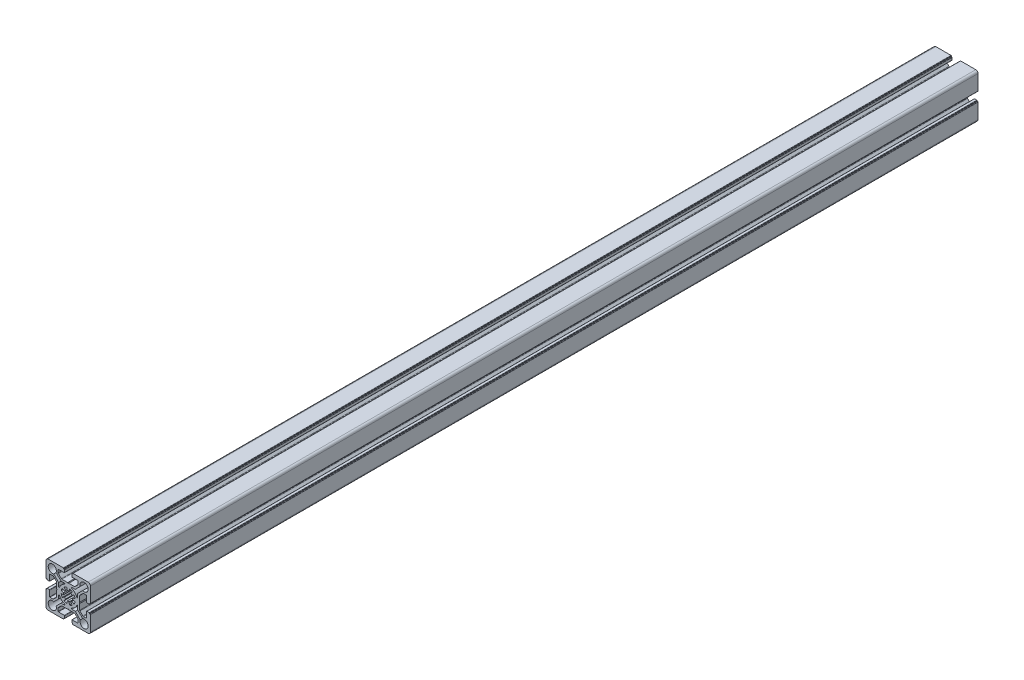
SolidWorks part; units mm, degrees
material "6063 T5"
ref_plane "Спереди" through (0, 0, 0) normal (0, 0, 1) x (1, 0, 0)
ref_plane "Сверху" through (0, 0, 0) normal (0, 1, 0) x (1, 0, 0)
ref_plane "Справа" through (0, 0, 0) normal (1, 0, 0) x (0, 0, -1)
sketch "Эскиз2" plane through (0, 0, 0) normal (0, 0, 1) x (1, 0, 0)
  line L0 (0, 0) -> (-21.2527, 21.2527) construction
  line L1 (-10.7, 8.013) -> (-10.7, 4.1183)
  line L2 (-10.7, 8.013) -> (-16.2812, 13.5942)
  line L3 (-8.013, 10.7) -> (-13.5942, 16.2812)
  line L4 (-8.013, 10.7) -> (-4.1183, 10.7)
  line L5 (10.7, 8.013) -> (16.2812, 13.5942)
  line L6 (10.7, 8.013) -> (10.7, 4.1183)
  line L7 (8.013, 10.7) -> (4.1183, 10.7)
  line L8 (8.013, 10.7) -> (13.5942, 16.2812)
  line L9 (8.013, -10.7) -> (13.5942, -16.2812)
  line L10 (8.013, -10.7) -> (4.1183, -10.7)
  line L11 (10.7, -8.013) -> (10.7, -4.1183)
  line L12 (10.7, -8.013) -> (16.2812, -13.5942)
  line L13 (-10.7, -8.013) -> (-16.2812, -13.5942)
  line L14 (-10.7, -8.013) -> (-10.7, -4.1183)
  line L15 (-8.013, -10.7) -> (-4.1183, -10.7)
  line L16 (-8.013, -10.7) -> (-13.5942, -16.2812)
  line L17 (-25, 11.3) -> (-25, 22.5)
  line L18 (-22.5, 25) -> (-11.3, 25)
  line L19 (11.3, 25) -> (22.5, 25)
  line L20 (25, 22.5) -> (25, 11.3)
  line L21 (25, -11.3) -> (25, -22.5)
  line L22 (22.5, -25) -> (11.3, -25)
  line L23 (-11.3, -25) -> (-22.5, -25)
  line L24 (-25, -22.5) -> (-25, -11.3)
  arc A2 (-3.9311, 9.7364) -> (-9.7364, 3.9311) centre (0, 0) ccw
  arc A3 (-9.7364, 3.9311) -> (-10.7, 4.1183) centre (-10.2, 4.1183) cw
  arc A4 (-16.2812, 13.5942) -> (-13.5942, 16.2812) centre (-17.9, 17.9) cw
  arc A5 (-3.9311, 9.7364) -> (-4.1183, 10.7) centre (-4.1183, 10.2) ccw
  arc A6 (13.5942, 16.2812) -> (16.2812, 13.5942) centre (17.9, 17.9) cw
  arc A7 (9.7364, 3.9311) -> (10.7, 4.1183) centre (10.2, 4.1183) ccw
  arc A8 (9.7364, 3.9311) -> (3.9311, 9.7364) centre (0, 0) ccw
  arc A9 (3.9311, 9.7364) -> (4.1183, 10.7) centre (4.1183, 10.2) cw
  arc A10 (16.2812, -13.5942) -> (13.5942, -16.2812) centre (17.9, -17.9) cw
  arc A11 (3.9311, -9.7364) -> (4.1183, -10.7) centre (4.1183, -10.2) ccw
  arc A12 (3.9311, -9.7364) -> (9.7364, -3.9311) centre (0, 0) ccw
  arc A13 (9.7364, -3.9311) -> (10.7, -4.1183) centre (10.2, -4.1183) cw
  arc A14 (-13.5942, -16.2812) -> (-16.2812, -13.5942) centre (-17.9, -17.9) cw
  arc A15 (-9.7364, -3.9311) -> (-10.7, -4.1183) centre (-10.2, -4.1183) ccw
  arc A16 (-9.7364, -3.9311) -> (-3.9311, -9.7364) centre (0, 0) ccw
  arc A17 (-3.9311, -9.7364) -> (-4.1183, -10.7) centre (-4.1183, -10.2) cw
  arc A18 (-25, 22.5) -> (-22.5, 25) centre (-22.5, 22.5) cw
  arc A19 (22.5, 25) -> (25, 22.5) centre (22.5, 22.5) cw
  arc A20 (25, -22.5) -> (22.5, -25) centre (22.5, -22.5) cw
  arc A21 (-22.5, -25) -> (-25, -22.5) centre (-22.5, -22.5) cw
  point P50 (0, 0)
  point P71 (0, 0)
  line B0 (-25, 11.3) -> (-25, 5.4)
  line B1 (-24.7, 5.1) -> (-24, 5.1)
  line B2 (-24, 5.1) -> (-24, 4.4)
  line B3 (-23.7, 4.1) -> (-21.1, 4.1)
  line B4 (-20.8, 4.4) -> (-20.8, 11)
  line B5 (-20.5, 11.3) -> (-17.2142, 11.3)
  line B6 (-16.5071, 11.0071) -> (-13.2929, 7.7929)
  line B7 (-13, 7.0858) -> (-13, 0.6)
  line B8 (-13, 0) -> (-25, 0) construction
  line B9 (-16.5071, -11.0071) -> (-13.2929, -7.7929)
  line B10 (-20.5, -11.3) -> (-17.2142, -11.3)
  line B11 (-20.8, -4.4) -> (-20.8, -11)
  line B12 (-23.7, -4.1) -> (-21.1, -4.1)
  line B13 (-24, -5.1) -> (-24, -4.4)
  line B14 (-24.7, -5.1) -> (-24, -5.1)
  line B15 (-25, -11.3) -> (-25, -5.4)
  line B16 (-13, 0.6) -> (-12.4, 0)
  line B17 (-12.4, 0) -> (-13, -0.6)
  line B18 (-13, -0.6) -> (-13, -7.0858)
  arc B19 (-21.1, 4.1) -> (-20.8, 4.4) centre (-21.1, 4.4) ccw
  arc B20 (-24, 4.4) -> (-23.7, 4.1) centre (-23.7, 4.4) ccw
  arc B21 (-25, 5.4) -> (-24.7, 5.1) centre (-24.7, 5.4) ccw
  arc B22 (-13.2929, 7.7929) -> (-13, 7.0858) centre (-14, 7.0858) cw
  arc B23 (-17.2142, 11.3) -> (-16.5071, 11.0071) centre (-17.2142, 10.3) cw
  arc B24 (-17.2142, -11.3) -> (-16.5071, -11.0071) centre (-17.2142, -10.3) ccw
  arc B25 (-13.2929, -7.7929) -> (-13, -7.0858) centre (-14, -7.0858) ccw
  arc B26 (-25, -5.4) -> (-24.7, -5.1) centre (-24.7, -5.4) cw
  arc B27 (-24, -4.4) -> (-23.7, -4.1) centre (-23.7, -4.4) cw
  arc B28 (-21.1, -4.1) -> (-20.8, -4.4) centre (-21.1, -4.4) cw
  arc B29 (-20.5, -11.3) -> (-20.8, -11) centre (-20.5, -11) cw
  arc B30 (-20.8, 11) -> (-20.5, 11.3) centre (-20.5, 11) cw
  line B31 (0, 0) -> (3.6062, 3.6062) construction
  line B32 (1.4579, 7.866) -> (0.9294, 5.0146)
  line B33 (2.8887, 4.203) -> (4.5312, 6.593)
  line B34 (0, 0) -> (0, 5.1) construction
  arc B35 (0.9294, -5.0146) -> (-0.9294, -5.0146) centre (0, 0) cw
  arc B36 (-6.593, -4.5312) -> (-7.866, -1.4579) centre (0, 0) cw
  arc B37 (4.203, 2.8887) -> (2.8887, 4.203) centre (0, 0) ccw
  arc B38 (4.5312, 6.593) -> (1.4579, 7.866) centre (0, 0) ccw
  arc B39 (0.9294, 5.0146) -> (-0.9294, 5.0146) centre (0, 0) ccw
  line B40 (-1.4579, 7.866) -> (-0.9294, 5.0146)
  arc B41 (4.5312, -6.593) -> (1.4579, -7.866) centre (0, 0) cw
  arc B42 (-4.203, -2.8887) -> (-2.8887, -4.203) centre (0, 0) ccw
  line B43 (-2.8887, -4.203) -> (-4.5312, -6.593)
  line B44 (0, 0) -> (6.3318, 0) construction
  line B45 (4.203, 2.8887) -> (6.593, 4.5312)
  line B46 (7.866, 1.4579) -> (5.0146, 0.9294)
  line B47 (-7.866, 1.4579) -> (-5.0146, 0.9294)
  line B48 (-4.203, 2.8887) -> (-6.593, 4.5312)
  line B49 (-2.8887, 4.203) -> (-4.5312, 6.593)
  line B50 (7.866, -1.4579) -> (5.0146, -0.9294)
  line B51 (4.203, -2.8887) -> (6.593, -4.5312)
  line B52 (2.8887, -4.203) -> (4.5312, -6.593)
  line B53 (1.4579, -7.866) -> (0.9294, -5.0146)
  line B54 (-1.4579, -7.866) -> (-0.9294, -5.0146)
  line B55 (-4.203, -2.8887) -> (-6.593, -4.5312)
  line B56 (-7.866, -1.4579) -> (-5.0146, -0.9294)
  arc B57 (5.0146, 0.9294) -> (5.0146, -0.9294) centre (0, 0) cw
  arc B58 (6.593, 4.5312) -> (7.866, 1.4579) centre (0, 0) cw
  arc B59 (-5.0146, 0.9294) -> (-5.0146, -0.9294) centre (0, 0) ccw
  arc B60 (-6.593, 4.5312) -> (-7.866, 1.4579) centre (0, 0) ccw
  arc B61 (-4.203, 2.8887) -> (-2.8887, 4.203) centre (0, 0) cw
  arc B62 (-4.5312, 6.593) -> (-1.4579, 7.866) centre (0, 0) cw
  arc B63 (6.593, -4.5312) -> (7.866, -1.4579) centre (0, 0) ccw
  arc B64 (4.203, -2.8887) -> (2.8887, -4.203) centre (0, 0) cw
  arc B65 (-4.5312, -6.593) -> (-1.4579, -7.866) centre (0, 0) ccw
  line B66 (11.3, 25) -> (5.4, 25)
  line B67 (5.1, 24.7) -> (5.1, 24)
  line B68 (5.1, 24) -> (4.4, 24)
  line B69 (4.1, 23.7) -> (4.1, 21.1)
  line B70 (4.4, 20.8) -> (11, 20.8)
  line B71 (11.3, 20.5) -> (11.3, 17.2142)
  line B72 (11.0071, 16.5071) -> (7.7929, 13.2929)
  line B73 (7.0858, 13) -> (0.6, 13)
  line B74 (0, 13) -> (0, 25) construction
  line B75 (-11.0071, 16.5071) -> (-7.7929, 13.2929)
  line B76 (-11.3, 20.5) -> (-11.3, 17.2142)
  line B77 (-4.4, 20.8) -> (-11, 20.8)
  line B78 (-4.1, 23.7) -> (-4.1, 21.1)
  line B79 (-5.1, 24) -> (-4.4, 24)
  line B80 (-5.1, 24.7) -> (-5.1, 24)
  line B81 (-11.3, 25) -> (-5.4, 25)
  line B82 (0.6, 13) -> (0, 12.4)
  line B83 (0, 12.4) -> (-0.6, 13)
  line B84 (-0.6, 13) -> (-7.0858, 13)
  arc B85 (4.1, 21.1) -> (4.4, 20.8) centre (4.4, 21.1) ccw
  arc B86 (4.4, 24) -> (4.1, 23.7) centre (4.4, 23.7) ccw
  arc B87 (5.4, 25) -> (5.1, 24.7) centre (5.4, 24.7) ccw
  arc B88 (7.7929, 13.2929) -> (7.0858, 13) centre (7.0858, 14) cw
  arc B89 (11.3, 17.2142) -> (11.0071, 16.5071) centre (10.3, 17.2142) cw
  arc B90 (-11.3, 17.2142) -> (-11.0071, 16.5071) centre (-10.3, 17.2142) ccw
  arc B91 (-7.7929, 13.2929) -> (-7.0858, 13) centre (-7.0858, 14) ccw
  arc B92 (-5.4, 25) -> (-5.1, 24.7) centre (-5.4, 24.7) cw
  arc B93 (-4.4, 24) -> (-4.1, 23.7) centre (-4.4, 23.7) cw
  arc B94 (-4.1, 21.1) -> (-4.4, 20.8) centre (-4.4, 21.1) cw
  arc B95 (-11.3, 20.5) -> (-11, 20.8) centre (-11, 20.5) cw
  arc B96 (11, 20.8) -> (11.3, 20.5) centre (11, 20.5) cw
  line B97 (25, -11.3) -> (25, -5.4)
  line B98 (24.7, -5.1) -> (24, -5.1)
  line B99 (24, -5.1) -> (24, -4.4)
  line B100 (23.7, -4.1) -> (21.1, -4.1)
  line B101 (20.8, -4.4) -> (20.8, -11)
  line B102 (20.5, -11.3) -> (17.2142, -11.3)
  line B103 (16.5071, -11.0071) -> (13.2929, -7.7929)
  line B104 (13, -7.0858) -> (13, -0.6)
  line B105 (13, 0) -> (25, 0) construction
  line B106 (16.5071, 11.0071) -> (13.2929, 7.7929)
  line B107 (20.5, 11.3) -> (17.2142, 11.3)
  line B108 (20.8, 4.4) -> (20.8, 11)
  line B109 (23.7, 4.1) -> (21.1, 4.1)
  line B110 (24, 5.1) -> (24, 4.4)
  line B111 (24.7, 5.1) -> (24, 5.1)
  line B112 (25, 11.3) -> (25, 5.4)
  line B113 (13, -0.6) -> (12.4, 0)
  line B114 (12.4, 0) -> (13, 0.6)
  line B115 (13, 0.6) -> (13, 7.0858)
  arc B116 (21.1, -4.1) -> (20.8, -4.4) centre (21.1, -4.4) ccw
  arc B117 (24, -4.4) -> (23.7, -4.1) centre (23.7, -4.4) ccw
  arc B118 (25, -5.4) -> (24.7, -5.1) centre (24.7, -5.4) ccw
  arc B119 (13.2929, -7.7929) -> (13, -7.0858) centre (14, -7.0858) cw
  arc B120 (17.2142, -11.3) -> (16.5071, -11.0071) centre (17.2142, -10.3) cw
  arc B121 (17.2142, 11.3) -> (16.5071, 11.0071) centre (17.2142, 10.3) ccw
  arc B122 (13.2929, 7.7929) -> (13, 7.0858) centre (14, 7.0858) ccw
  arc B123 (25, 5.4) -> (24.7, 5.1) centre (24.7, 5.4) cw
  arc B124 (24, 4.4) -> (23.7, 4.1) centre (23.7, 4.4) cw
  arc B125 (21.1, 4.1) -> (20.8, 4.4) centre (21.1, 4.4) cw
  arc B126 (20.5, 11.3) -> (20.8, 11) centre (20.5, 11) cw
  arc B127 (20.8, -11) -> (20.5, -11.3) centre (20.5, -11) cw
  line B128 (-11.3, -25) -> (-5.4, -25)
  line B129 (-5.1, -24.7) -> (-5.1, -24)
  line B130 (-5.1, -24) -> (-4.4, -24)
  line B131 (-4.1, -23.7) -> (-4.1, -21.1)
  line B132 (-4.4, -20.8) -> (-11, -20.8)
  line B133 (-11.3, -20.5) -> (-11.3, -17.2142)
  line B134 (-11.0071, -16.5071) -> (-7.7929, -13.2929)
  line B135 (-7.0858, -13) -> (-0.6, -13)
  line B136 (0, -13) -> (0, -25) construction
  line B137 (11.0071, -16.5071) -> (7.7929, -13.2929)
  line B138 (11.3, -20.5) -> (11.3, -17.2142)
  line B139 (4.4, -20.8) -> (11, -20.8)
  line B140 (4.1, -23.7) -> (4.1, -21.1)
  line B141 (5.1, -24) -> (4.4, -24)
  line B142 (5.1, -24.7) -> (5.1, -24)
  line B143 (11.3, -25) -> (5.4, -25)
  line B144 (-0.6, -13) -> (0, -12.4)
  line B145 (0, -12.4) -> (0.6, -13)
  line B146 (0.6, -13) -> (7.0858, -13)
  arc B147 (-4.1, -21.1) -> (-4.4, -20.8) centre (-4.4, -21.1) ccw
  arc B148 (-4.4, -24) -> (-4.1, -23.7) centre (-4.4, -23.7) ccw
  arc B149 (-5.4, -25) -> (-5.1, -24.7) centre (-5.4, -24.7) ccw
  arc B150 (-7.7929, -13.2929) -> (-7.0858, -13) centre (-7.0858, -14) cw
  arc B151 (-11.3, -17.2142) -> (-11.0071, -16.5071) centre (-10.3, -17.2142) cw
  arc B152 (11.3, -17.2142) -> (11.0071, -16.5071) centre (10.3, -17.2142) ccw
  arc B153 (7.7929, -13.2929) -> (7.0858, -13) centre (7.0858, -14) ccw
  arc B154 (5.4, -25) -> (5.1, -24.7) centre (5.4, -24.7) cw
  arc B155 (4.4, -24) -> (4.1, -23.7) centre (4.4, -23.7) cw
  arc B156 (4.1, -21.1) -> (4.4, -20.8) centre (4.4, -21.1) cw
  arc B157 (11.3, -20.5) -> (11, -20.8) centre (11, -20.5) cw
  arc B158 (-11, -20.8) -> (-11.3, -20.5) centre (-11, -20.5) cw
  dimension "D1" = 25
  dimension "D2" = 45
  dimension "D3" = 0.5
  dimension "D4" = 10.5
  dimension "D7" = 4.6
  dimension "D9" = 2.5
  dimension "D5" = 2.3
  dimension "D6" = 1.9
  dimension "D8" = 4
  dimension "D10" = 7.1
sketch_block_instance "8B(20,5PL_cut)-1"
sketch_block "8B(20,5PL_cut)" parameters "D7"=0.3, "D8"=1, "D12"=0.3, "D10"=0.3, "D1"=12, "D2"=4.2, "D3"=8.2, "D4"=22.6, "D5"=10.2, "D6"=135, "D9"=1, "D11"=2.5, "D13"=1.2, "D14"=11.8
sketch_block_instance "Блок1-1"
sketch_block "Блок1" parameters "D1"=10.2, "D5"=16, "D2"=10.5, "D3"=24, "D4"=45
sketch_block_instance "8B(20,5PL_cut)-4"
sketch_block_instance "8B(20,5PL_cut)-5"
sketch_block_instance "8B(20,5PL_cut)-6"
extrude "Бобышка-Вытянуть2" add sketch "Эскиз2" along normal blind 1000 contours B156 B140 B155 B141 B142 B154 B143 L22 A20 L21 B97 B118 B98 B99 B117 B100 B116 B101 B127 B102 B120 B103 B119 B104 B113 B114 B115 B122 B106 B121 B107 B126 B108 B125 B109 B124 B110 B111 B123 B112 L20 A19 L19 B66 B87 B67 B68 B86 B69 B85 B70
